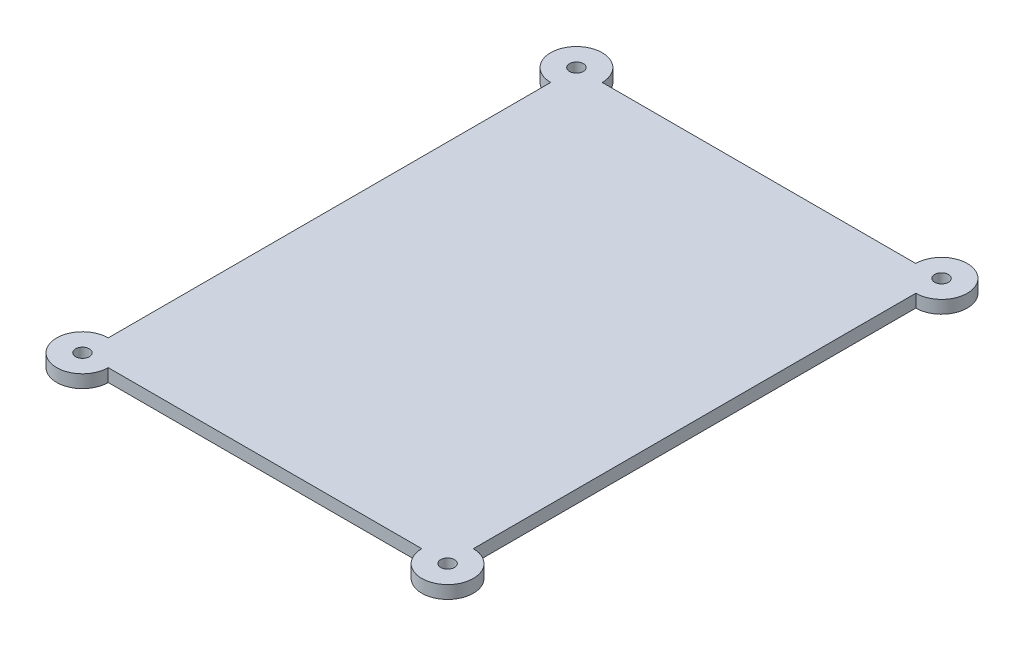
SolidWorks part; units mm, degrees
ref_plane "Front Plane" through (0, 0, 0) normal (0, 0, 1) x (1, 0, 0)
ref_plane "Top Plane" through (0, 0, 0) normal (0, 1, 0) x (1, 0, 0)
ref_plane "Right Plane" through (0, 0, 0) normal (1, 0, 0) x (0, 0, -1)
sketch "Sketch1" plane through (0, 0, 0) normal (0, 1, 0) x (1, 0, 0)
  line L1 (-42.5, -57.5) -> (42.5, -57.5)
  line L2 (-42.5, -57.5) -> (-42.5, 57.5)
  line L3 (-42.5, 57.5) -> (42.5, 57.5)
  line L4 (42.5, -57.5) -> (42.5, 57.5)
  line L5 (-37.9585, -51.3556) -> (38.9337, 52.6749) construction
  line L6 (-35.5557, 48.1047) -> (38.9337, -52.6749) construction
  arc A0 (42.5, 51.5) -> (36.5, 57.5) centre (42.5, 57.5) ccw
  arc A1 (-36.5, 57.5) -> (-42.5, 51.5) centre (-42.5, 57.5) ccw
  arc A2 (-42.5, -51.5) -> (-36.5, -57.5) centre (-42.5, -57.5) ccw
  arc A3 (36.5, -57.5) -> (42.5, -51.5) centre (42.5, -57.5) ccw
  point P0 (0, 0)
  dimension "D1" = 115
  dimension "D2" = 85
extrude "Boss-Extrude1" add sketch "Sketch1" along normal blind 3 contours L1 L4 L3 L2 | L2 A2 L1 | L1 A3 L4 | L4 A0 L3 | L3 A1 L2
sketch "Sketch2" plane through (0, 0, 0) normal (0, -1, 0) x (1, 0, 0)
  circle A0 centre (-42.5, 57.5) radius 1.6
  circle A1 centre (42.5, 57.5) radius 1.6
  circle A2 centre (42.5, -57.5) radius 1.6
  circle A3 centre (-42.5, -57.5) radius 1.6
  point P12 (0, 0)
  dimension "D1" = 3.2
extrude "Cut-Extrude1" cut sketch "Sketch2" against normal blind 40
